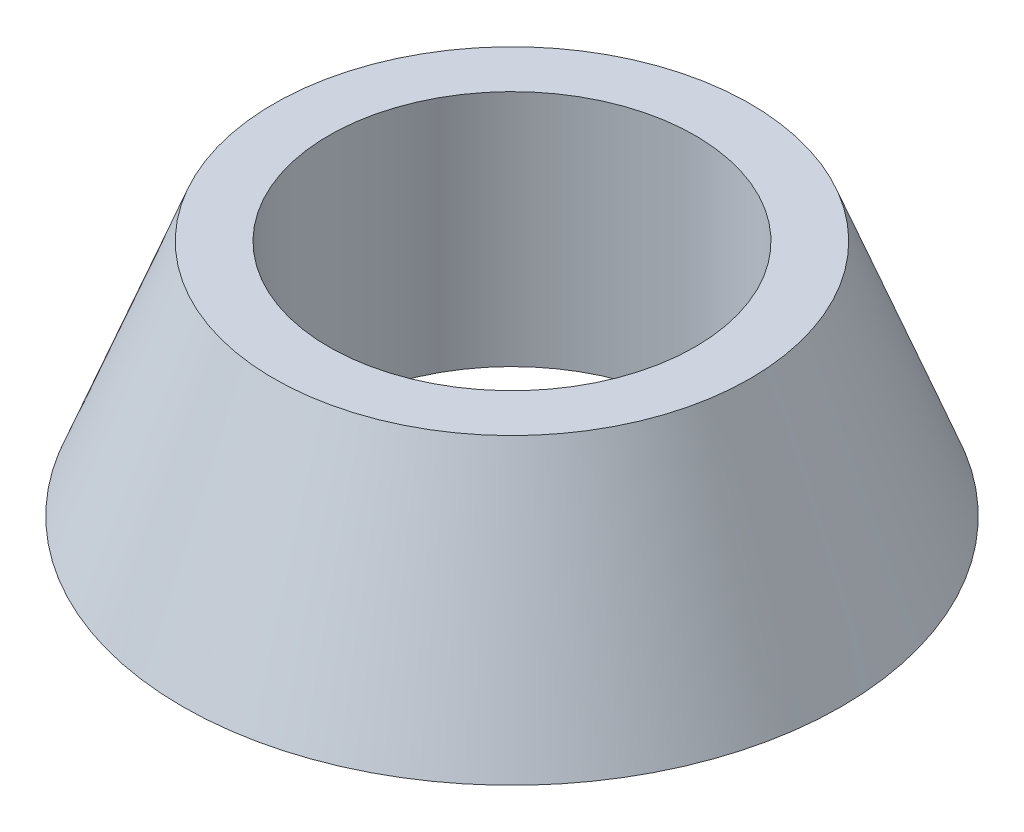
SolidWorks part; units mm, degrees
ref_plane "Płaszczyzna XY" through (0, 0, 0) normal (0, 0, 1) x (1, 0, 0)
ref_plane "Płaszczyzna XZ" through (0, 0, 0) normal (0, 1, 0) x (1, 0, 0)
ref_plane "Płaszczyzna YZ" through (0, 0, 0) normal (1, 0, 0) x (0, 0, -1)
sketch "Szkic1" plane through (0, 0, 0) normal (0, 0, 1) x (1, 0, 0)
  line L0 (0, 0) -> (0, 5.4167) construction
  line L1 (5, 0) -> (5, 6.5)
  line L3 (9, 0) -> (5, 0)
  line L4 (5, 6.5) -> (6.5, 6.5)
  line L5 (6.5, 6.5) -> (9, 0)
  dimension "D1" = 6.5
  dimension "D2" = 5
  dimension "D3" = 9
  dimension "D4" = 1.5
revolve "Obrót1" add sketch "Szkic1" angle 360 about L0
